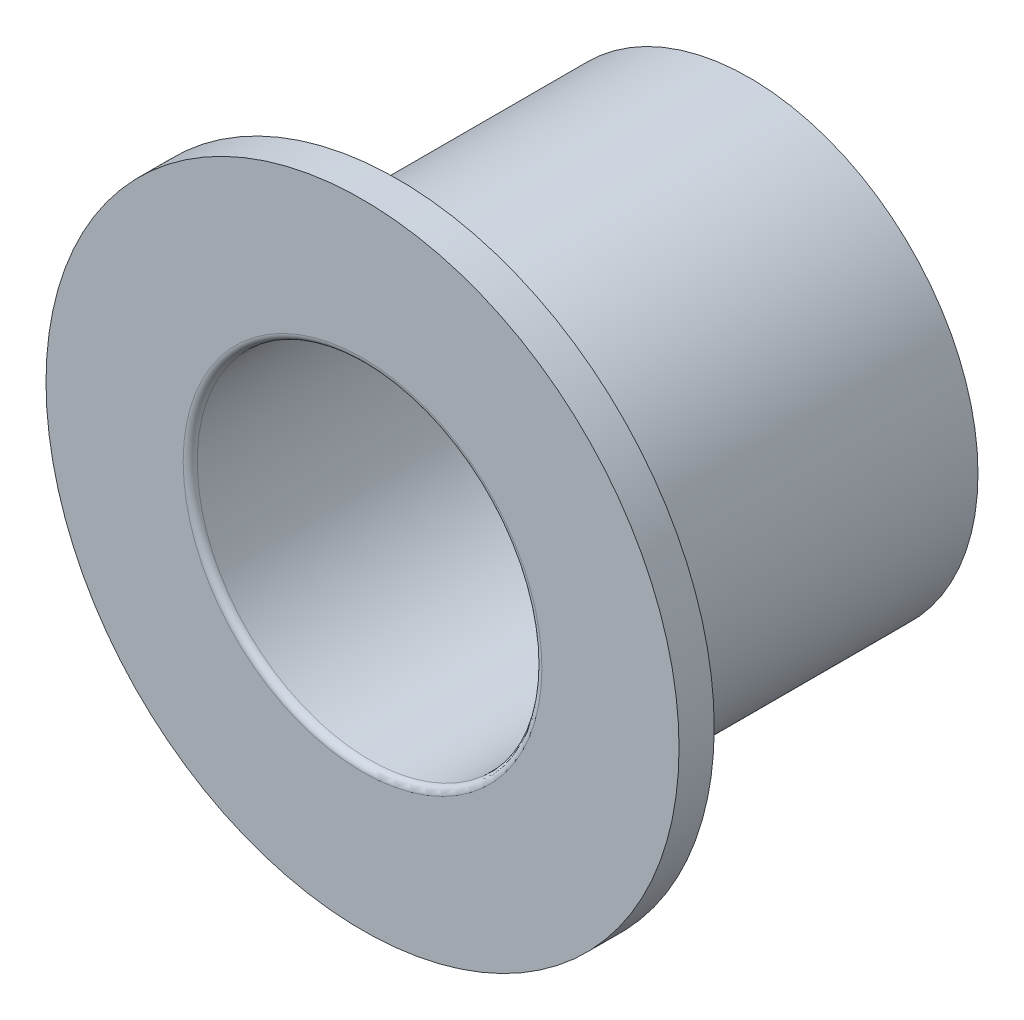
SolidWorks part; units mm, degrees
material "AISI 316 Stainless Steel Sheet (SS)"
ref_plane "Front Plane" through (0, 0, 0) normal (0, 0, 1) x (1, 0, 0)
ref_plane "Top Plane" through (0, 0, 0) normal (0, 1, 0) x (1, 0, 0)
ref_plane "Right Plane" through (0, 0, 0) normal (1, 0, 0) x (0, 0, -1)
sketch "Sketch1" plane through (0, 0, 0) normal (0, 0, 1) x (1, 0, 0)
  circle A0 centre (0, 0) radius 1.651
  dimension "D1" = 3.302
extrude "Boss-Extrude1" add sketch "Sketch1" along normal blind 2.54 contours A0
sketch "Sketch2" plane through (0, 0, 2.54) normal (0, 0, 1) x (1, 0, 0)
  circle A0 centre (0, 0) radius 2.286
  dimension "D1" = 4.572
extrude "Boss-Extrude2" add sketch "Sketch2" along normal blind 0.254
sketch "Sketch3" plane through (0, 0, 0) normal (0, 0, -1) x (-1, 0, 0)
  circle A0 centre (0, 0) radius 1.2446
  dimension "D1" = 2.4892
extrude "Cut-Extrude3" cut sketch "Sketch3" against normal through all and the other way through all contours A0
sketch "Sketch6" plane through (0, 0, 2.794) normal (0, 0, 1) x (1, 0, 0)
  circle A0 centre (0, 0) radius 1.2446 construction
  circle A1 centre (0, 0) radius 1.2446
fillet "Fillet3" radius 0.0508 1 edges at (-1.2446, 0, 2.794)
